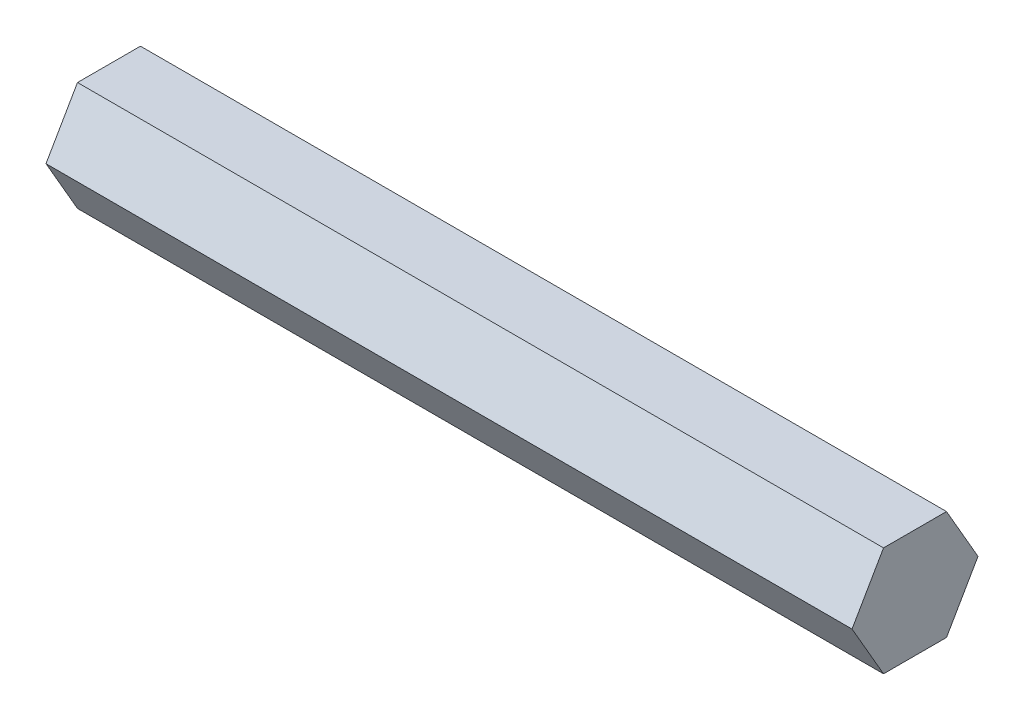
SolidWorks part; units mm, degrees
ref_plane "Front Plane" through (0, 0, 0) normal (0, 0, 1) x (1, 0, 0)
ref_plane "Top Plane" through (0, 0, 0) normal (0, 1, 0) x (1, 0, 0)
ref_plane "Right Plane" through (0, 0, 0) normal (1, 0, 0) x (0, 0, -1)
sketch "Sketch1" plane through (0, 0, 0) normal (1, 0, 0) x (0, 0, -1)
  line L1 (7.3323, 0) -> (3.6662, 6.35)
  line L2 (3.6662, 6.35) -> (-3.6662, 6.35)
  line L3 (-3.6662, 6.35) -> (-7.3323, 0)
  line L4 (-7.3323, 0) -> (-3.6662, -6.35)
  line L5 (-3.6662, -6.35) -> (3.6662, -6.35)
  line L6 (3.6662, -6.35) -> (7.3323, 0)
  circle A0 centre (0, 0) radius 6.35 construction
  dimension "D1" = 12.7
extrude "Boss-Extrude1" add sketch "Sketch1" along normal blind 93.85
